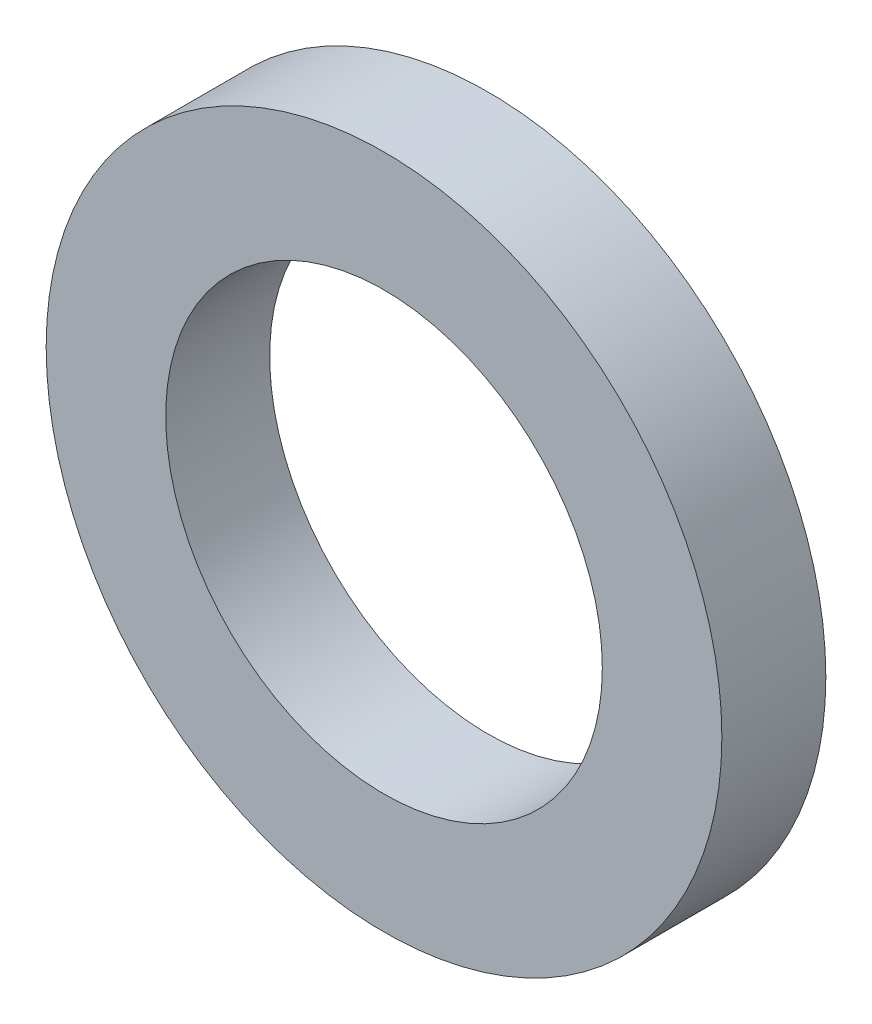
SolidWorks part; units mm, degrees
ref_plane "Front Plane" through (0, 0, 0) normal (0, 0, 1) x (1, 0, 0)
ref_plane "Top Plane" through (0, 0, 0) normal (0, 1, 0) x (1, 0, 0)
ref_plane "Right Plane" through (0, 0, 0) normal (1, 0, 0) x (0, 0, -1)
sketch "Sketch1" plane through (0, 0, 0) normal (0, 0, 1) x (1, 0, 0)
  circle A0 centre (0, 0) radius 4.2
  circle A1 centre (0, 0) radius 6.5
  dimension "D1" = 8.4
  dimension "D2" = 13
extrude "Boss-Extrude1" add sketch "Sketch1" along normal blind 2
